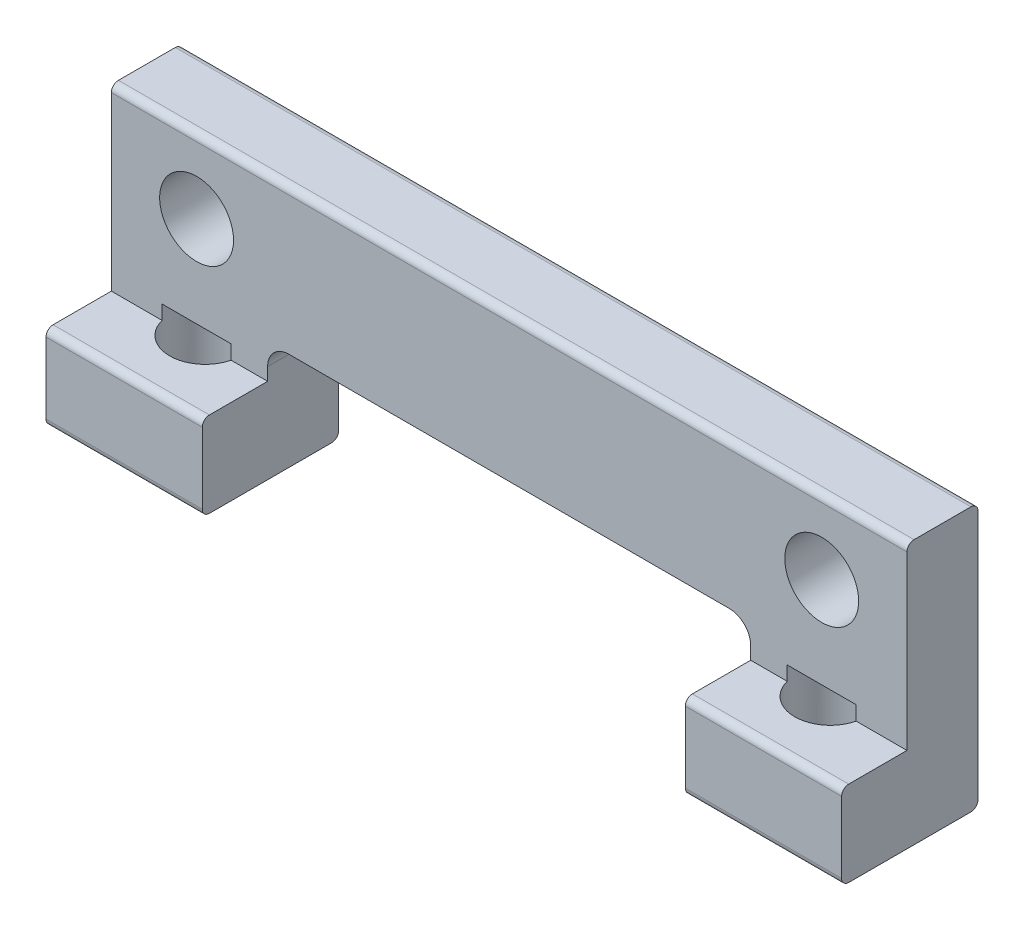
SolidWorks part; units mm, degrees
ref_plane "정면" through (0, 0, 0) normal (0, 0, 1) x (1, 0, 0)
ref_plane "윗면" through (0, 0, 0) normal (0, 1, 0) x (1, 0, 0)
ref_plane "우측면" through (0, 0, 0) normal (1, 0, 0) x (0, 0, -1)
sketch "스케치1" plane through (0, 0, 0) normal (0, 0, 1) x (1, 0, 0)
  line L1 (0, 0) -> (28, 0)
  line L2 (0, 0) -> (0, 9.3)
  line L3 (0, 9.3) -> (28, 9.3)
  line L4 (28, 0) -> (28, 9.3)
  dimension "D1" = 9.3
  dimension "D2" = 28
extrude "보스-돌출1" add sketch "스케치1" along normal blind 4.8
sketch "스케치2" plane through (0, 0, 4.8) normal (0, 0, 1) x (1, 0, 0)
  line L0 (0, 9.3) -> (0, 0) construction
  line L1 (0, 3) -> (28, 3)
  line L2 (0, 3) -> (0, 9.3)
  line L3 (0, 9.3) -> (28, 9.3)
  line L4 (28, 3) -> (28, 9.3)
  dimension "D1" = 6.3
extrude "컷-돌출1" cut sketch "스케치2" against normal blind 2.3
sketch "스케치4" plane through (0, 0, 4.8) normal (0, 0, 1) x (1, 0, 0)
  line L0 (0, 0) -> (28, 0) construction
  line L1 (5.5, 0) -> (22.5, 0)
  line L2 (5.5, 0) -> (5.5, 4.2)
  line L3 (5.5, 4.2) -> (22.5, 4.2)
  line L4 (22.5, 0) -> (22.5, 4.2)
  line L5 (0, 3) -> (0, 0) construction
  dimension "D1" = 17
  dimension "D2" = 5.5
  dimension "D3" = 4.2
extrude "컷-돌출2" cut sketch "스케치4" against normal through all both and the other way through all
sketch "스케치5" plane through (0, 0, 2.5) normal (0, 0, 1) x (1, 0, 0)
  line L0 (14, -2.9549) -> (14, 13.7298) construction
  line L1 (28, 9.3) -> (0, 9.3) construction
  circle A0 centre (3, 6.7) radius 1.3
  circle A1 centre (25, 6.7) radius 1.3
  dimension "D1" = 2.6
  dimension "D2" = 2.6
  dimension "D3" = 11
extrude "컷-돌출3" cut sketch "스케치5" against normal through all
fillet "필렛1" radius 0.75 2 edges at (22.5, 4.2, 1.25) (5.5, 4.2, 1.25)
sketch "스케치6" plane through (0, 0, 0) normal (0, -1, 0) x (1, 0, 0)
  line L0 (14, 2.5) -> (14, -4.7304) construction
  line L1 (6.25, 2.5) -> (21.75, 2.5) construction
  line L2 (0, 0) -> (5.5, 0) construction
  circle A0 centre (3, 2.2) radius 1.25
  circle A1 centre (25, 2.2) radius 1.25
  dimension "D1" = 2.5
  dimension "D2" = 2.2
  dimension "D3" = 11
extrude "컷-돌출4" cut sketch "스케치6" against normal blind 3.5
fillet "필렛2" radius 0.25 8 edges at (14, 9.3, 0) (14, 9.3, 2.5) (25.25, 3, 4.8) (2.75, 3, 4.8) (25.25, 0, 0) (25.25, 0, 4.8) (2.75, 0, 0) (2.75, 0, 4.8)
